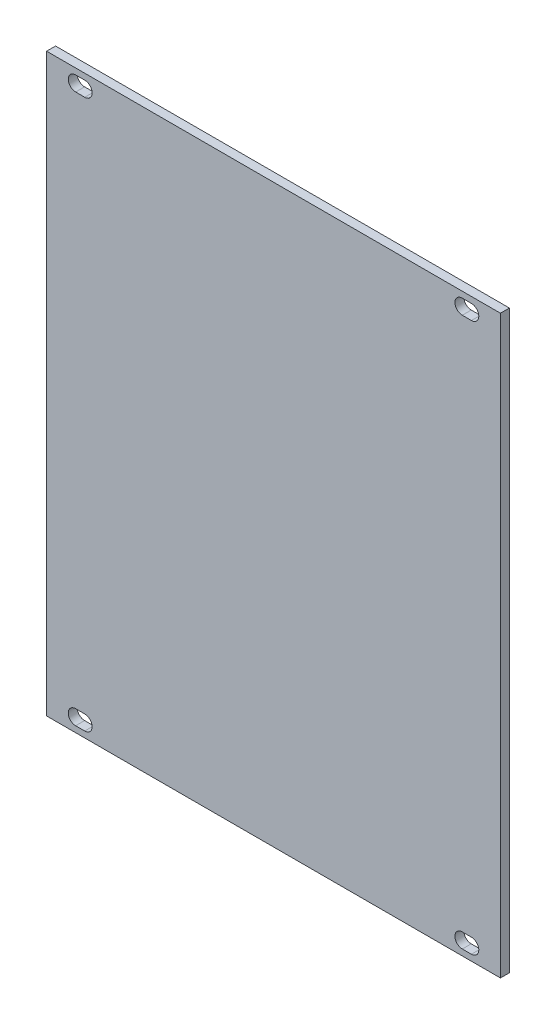
SolidWorks part; units mm, degrees
ref_plane "Front Plane" through (0, 0, 0) normal (0, 0, 1) x (1, 0, 0)
ref_plane "Top Plane" through (0, 0, 0) normal (0, 1, 0) x (1, 0, 0)
ref_plane "Right Plane" through (0, 0, 0) normal (1, 0, 0) x (0, 0, -1)
sketch "Sketch1" plane through (0, 0, 0) normal (0, 0, 1) x (1, 0, 0)
  line L0 (-43.15, 64.25) -> (-43.15, -64.25) construction
  line L1 (-50.65, 64.25) -> (50.65, 64.25)
  line L2 (-50.65, 64.25) -> (-50.65, -64.25)
  line L3 (-50.65, -64.25) -> (50.65, -64.25)
  line L4 (50.65, 64.25) -> (50.65, -64.25)
  line L5 (-50.65, 64.25) -> (50.65, -64.25) construction
  line L6 (-50.65, -64.25) -> (50.65, 64.25) construction
  line L7 (-50.65, 61.25) -> (50.65, 61.25) construction
  line L8 (-50.65, -61.25) -> (50.65, -61.25) construction
  line L9 (-44.166, -61.25) -> (-42.134, -61.25) construction
  line L10 (42.134, 61.25) -> (44.166, 61.25) construction
  line L11 (-44.166, -59.6) -> (-42.134, -59.6)
  line L12 (-44.166, -62.9) -> (-42.134, -62.9)
  line L13 (-44.166, 61.25) -> (-42.134, 61.25) construction
  line L14 (-44.166, 62.9) -> (-42.134, 62.9)
  line L15 (-44.166, 59.6) -> (-42.134, 59.6)
  line L16 (42.134, 62.9) -> (44.166, 62.9)
  line L17 (42.134, 59.6) -> (44.166, 59.6)
  line L18 (42.134, -61.25) -> (44.166, -61.25) construction
  line L19 (42.134, -59.6) -> (44.166, -59.6)
  line L20 (42.134, -62.9) -> (44.166, -62.9)
  line L21 (43.15, 64.25) -> (43.15, -64.25) construction
  arc A0 (-44.166, -59.6) -> (-44.166, -62.9) centre (-44.166, -61.25) ccw
  arc A1 (-42.134, -62.9) -> (-42.134, -59.6) centre (-42.134, -61.25) ccw
  arc A2 (-44.166, 62.9) -> (-44.166, 59.6) centre (-44.166, 61.25) ccw
  arc A3 (-42.134, 59.6) -> (-42.134, 62.9) centre (-42.134, 61.25) ccw
  arc A4 (42.134, 62.9) -> (42.134, 59.6) centre (42.134, 61.25) ccw
  arc A5 (44.166, 59.6) -> (44.166, 62.9) centre (44.166, 61.25) ccw
  arc A6 (42.134, -59.6) -> (42.134, -62.9) centre (42.134, -61.25) ccw
  arc A7 (44.166, -62.9) -> (44.166, -59.6) centre (44.166, -61.25) ccw
  point P0 (0, 0)
  point P8 (43.15, 61.25)
  point P18 (-43.15, -61.25)
  point P24 (-43.15, 61.25)
  point P34 (43.15, -61.25)
  point P42 (0, 0)
  point P43 (0, 0)
  dimension "D6" = 1.65
  dimension "D7" = 1.65
  dimension "D11" = 1.65
  dimension "D13" = 1.65
  dimension "D1" = 128.5
  dimension "D2" = 101.3
  dimension "D3" = 7.5
  dimension "D4" = 3
  dimension "D8" = 2.032
  dimension "D9" = 2.032
  dimension "D10" = 7.5
  dimension "D12" = 2.032
  dimension "D14" = 2.032
  dimension "D5" = 3
extrude "Boss-Extrude1" add sketch "Sketch1" along normal blind 2
